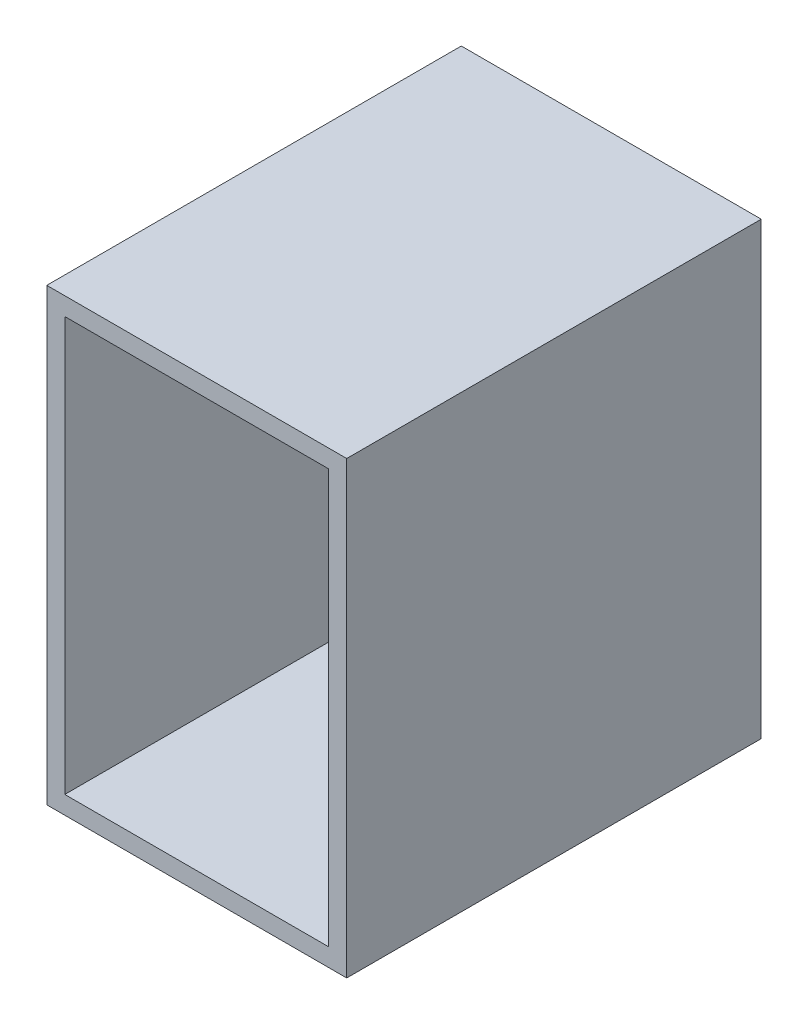
SolidWorks part; units mm, degrees
material "Plain Carbon Steel"
ref_plane "Front Plane" through (0, 0, 0) normal (0, 0, 1) x (1, 0, 0)
ref_plane "Top Plane" through (0, 0, 0) normal (0, 1, 0) x (1, 0, 0)
ref_plane "Right Plane" through (0, 0, 0) normal (1, 0, 0) x (0, 0, -1)
sketch "Sketch1" plane through (0, 0, 0) normal (0, 0, 1) x (1, 0, 0)
  line B0 (-50, -75) -> (50, -75)
  line B1 (-50, -75) -> (-50, 75)
  line B2 (50, -75) -> (50, 75)
  line B3 (-50, 75) -> (50, 75)
  line B4 (-44, -69) -> (44, -69)
  line B5 (-44, -69) -> (-44, 69)
  line B6 (44, -69) -> (44, 69)
  line B7 (-44, 69) -> (44, 69)
sketch_block_instance "15x10x6_profil-1"
sketch_block "15x10x6_profil" parameters "D1"=100, "D2"=150, "D3"=6, "D4"=6
extrude "Boss-Extrude1" add sketch "Sketch1" along normal blind 138.2023
